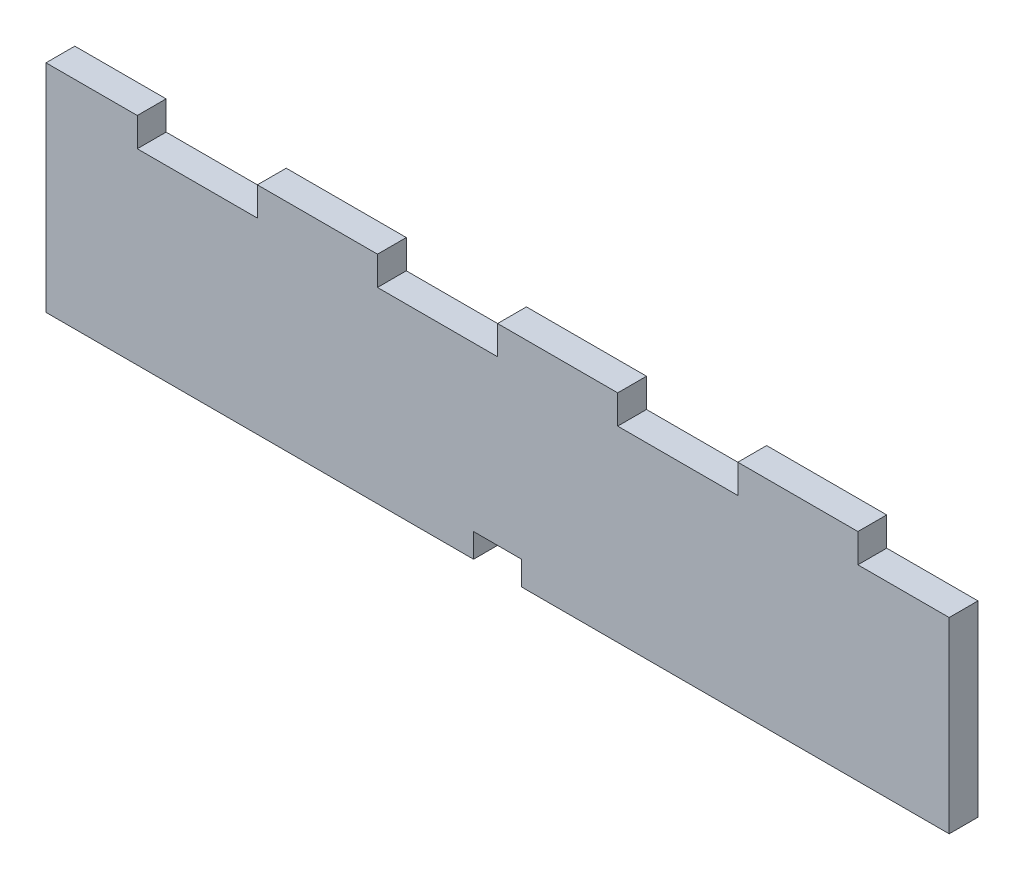
SolidWorks part; units mm, degrees
ref_plane "Plano frontal" through (0, 0, 0) normal (0, 0, 1) x (1, 0, 0)
ref_plane "Plano superior" through (0, 0, 0) normal (0, 1, 0) x (1, 0, 0)
ref_plane "Plano direito" through (0, 0, 0) normal (1, 0, 0) x (0, 0, -1)
sketch "Esboço1" plane through (0, 0, 0) normal (0, 0, 1) x (1, 0, 0)
  line L1 (0, 0) -> (188, 0)
  line L2 (0, 0) -> (0, 39)
  line L3 (19, 39) -> (44, 39)
  line L4 (188, 0) -> (188, 39)
  line L6 (0, 39) -> (0, 45)
  line L7 (0, 45) -> (19, 45)
  line L8 (19, 39) -> (19, 45)
  line L9 (19, 39) -> (44, 39)
  line L14 (44, 39) -> (44, 45)
  line L15 (44, 45) -> (69, 45)
  line L16 (69, 39) -> (69, 45)
  line L17 (94, 39) -> (94, 45)
  line L18 (94, 45) -> (119, 45)
  line L19 (119, 39) -> (119, 45)
  line L21 (144, 39) -> (144, 45)
  line L22 (144, 45) -> (169, 45)
  line L23 (169, 39) -> (169, 45)
  line L24 (69, 39) -> (94, 39)
  line L25 (119, 39) -> (144, 39)
  line L26 (169, 39) -> (188, 39)
  line L27 (94, 0) -> (94, 39) construction
  line L29 (94, 0) -> (99, 0)
  line L30 (94, 0) -> (94, 5)
  line L31 (94, 5) -> (99, 5)
  line L32 (99, 0) -> (99, 5)
  line L33 (94, 5) -> (89, 5)
  line L34 (94, 5) -> (94, 0)
  line L35 (94, 0) -> (89, 0)
  line L36 (89, 5) -> (89, 0)
  dimension "D1" = 39
  dimension "D2" = 188
  dimension "D3" = 6
  dimension "D4" = 19
  dimension "D5" = 5
  dimension "D6" = 25
  dimension "D7" = 6
  dimension "D8" = 25
  dimension "D10" = 5
  dimension "D9" = 3
extrude "Ressalto-extrusão1" add sketch "Esboço1" along normal blind 6 contours L33 L27 L24 L16 L15 L14 L3 L8 L7 L6 L2 L1 L36 | L27 L31 L32 L1 L4 L26 L23 L22 L21 L25 L19 L18 L17
